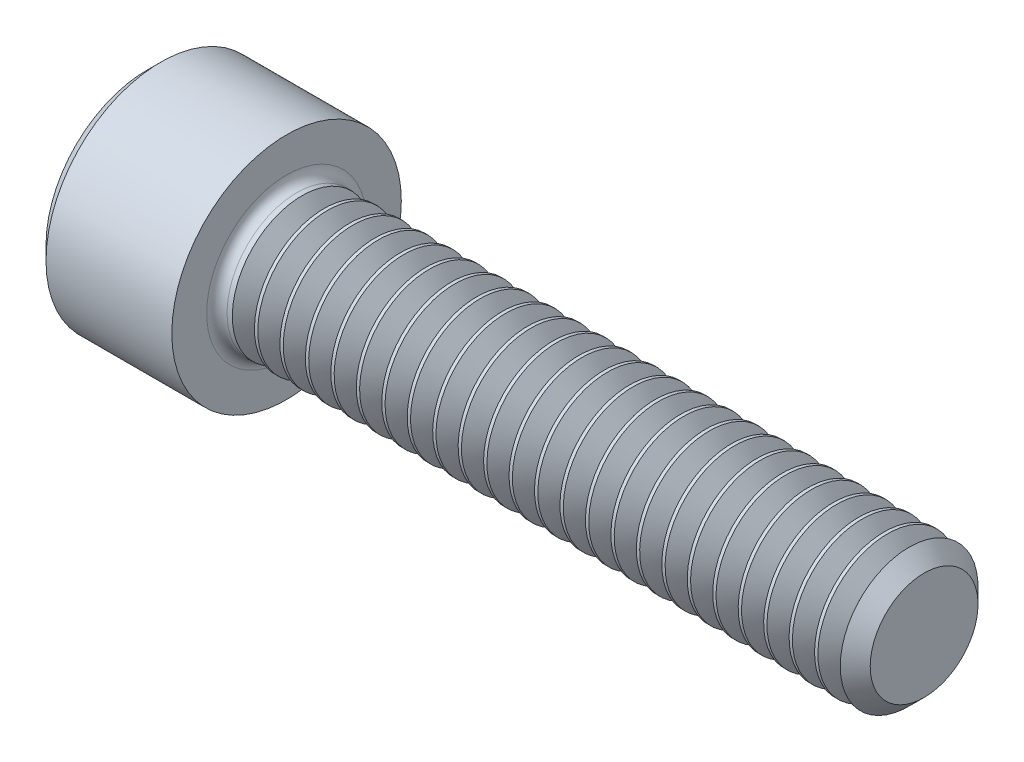
SolidWorks part; units mm, degrees
ref_plane "Plane1" through (0, 0, 0) normal (0, 0, 1) x (1, 0, 0)
ref_plane "Plane2" through (0, 0, 0) normal (0, 1, 0) x (1, 0, 0)
ref_plane "Plane3" through (0, 0, 0) normal (1, 0, 0) x (0, 0, -1)
sketch "BodySke" plane through (0, 0, 0) normal (0, 0, 1) x (1, 0, 0)
  line L0 (0, 0) -> (0, 3.0226)
  line L1 (0.4064, 3.429) -> (4.1656, 3.429)
  line L2 (4.1656, 3.429) -> (4.1656, 2.0828)
  line L3 (4.1656, 2.0828) -> (22.7432, 2.0828)
  line L4 (23.2156, 1.6104) -> (23.2156, 0)
  line L5 (23.2156, 0) -> (0, 0)
  line L6 (-31.75, 0) -> (127, 0) construction
  line L7 (0, 3.0226) -> (0.4064, 3.429)
  line L8 (23.2156, 1.6104) -> (22.7432, 2.0828)
  line L9 (0, -3.0226) -> (0.4064, -3.429) construction
  line L10 (23.2156, -1.6104) -> (22.7432, -2.0828) construction
  line L11 (4.9581, 9.525) -> (4.9581, 3.175) construction
  line L12 (4.1656, 9.525) -> (4.1656, 3.175) construction
  line L13 (-14.8844, 9.525) -> (-14.8844, 3.175) construction
  dimension "Diameter" = 4.1656
  dimension "Head_ht" = 4.1656
  dimension "Length" = 19.05
  dimension "Body_ch_ang" = 45
  dimension "Head_dia" = 6.858
  dimension "Head_ch_ang" = 45
  dimension "Head_side_ht" = 3.7592
  dimension "Minor_dia" = 3.2207
  dimension "Advance" = 0.7925
  dimension "Thread_nom" = 19.05
  dimension "Thread_length" = 38.1
revolve "Base-Revolve" add sketch "BodySke"
cosmetic thread "ThreadCosmetic" [suppressed]
fillet "Fillet1" radius 0.3048 1 edges at (4.1656, 0, 2.0828)
sketch "Sketch2" plane through (0, 0, 0) normal (0, 0, 1) x (1, 0, 0)
  line L0 (0, 1.778) -> (1.9558, 1.778)
  line L1 (1.9558, 1.778) -> (2.9823, 0)
  line L2 (-31.75, 0) -> (127, 0) construction
  line L3 (2.9823, 0) -> (0, 0)
  line L4 (0, 0) -> (0, 1.778)
  line L5 (0, 3.0226) -> (0, -3.0226) construction
  line L6 (0, 0) -> (47.625, 0) construction
  line L7 (4.1656, -3.429) -> (4.1656, 3.429) construction
  dimension "D1" = 1.778
  dimension "D2" = 60
  dimension "Wall_thickness" = 2.2098
revolve "Hex-PreBroach" cut sketch "Sketch2" angle 360 about L6
sketch "Sketch3" plane through (0, 0, 0) normal (-1, 0, 0) x (0, 0.5, 0.866)
  line L0 (1.0265, 1.778) -> (-1.0265, 1.778)
  line L1 (-1.0265, 1.778) -> (-2.0531, 0)
  line L2 (1.0265, 1.778) -> (2.0531, 0)
  line L3 (1.0265, -1.778) -> (2.0531, 0)
  line L4 (1.0265, -1.778) -> (-1.0265, -1.778)
  line L5 (-1.0265, -1.778) -> (-2.0531, 0)
  dimension "D1" = 1.778
  dimension "D2" = 1.778
  dimension "Hex_size" = 3.556
extrude "Hex" cut sketch "Sketch3" against normal blind 1.9558
sketch "Sketch4" plane through (0, 0, 0) normal (-1, 0, 0) x (0, 0, 1)
  line L0 (0, 0) -> (2.1971, 0)
  line L1 (0, 0) -> (6.1484, 3.5498) construction
  line L2 (0, 0) -> (1.0985, 1.9027)
  line L3 (1.8302, 0.5287) -> (2.0897, 0.6786)
  line L4 (1.373, 1.3206) -> (1.6325, 1.4704)
  arc A0 (1.8302, 0.5287) -> (1.373, 1.3206) centre (0, 0) ccw
  arc A1 (2.1971, 0) -> (2.0897, 0.6786) centre (0, 0) ccw
  arc A2 (1.0985, 1.9027) -> (1.6325, 1.4704) centre (0, 0) cw
  dimension "D1" = 30
  dimension "Spline_n_dim" = 3.81
  dimension "Spline_m_dim" = 4.3942
  dimension "D2" = 60
  dimension "D3" = 0.4572
  dimension "Spline_p_dim" = 0.9144
extrude "Spline" [suppressed] cut sketch "Sketch4" against normal blind 1.9558
pattern_circular "CirPattern1" [suppressed] count 6 every 60
sketch "Sketch5" plane through (0, 0, 0) normal (0, 0, 1) x (1, 0, 0)
  line L0 (-31.75, 0) -> (127, 0) construction
  line L2 (0, 3.0226) -> (0, -3.0226) construction
  circle A0 centre (1.524, 0) radius 0.5905
  dimension "Drilled_hole_dia" = 1.1811
  dimension "Drilled_hole_loc" = 1.524
extrude "Hole" [suppressed] cut sketch "Sketch5" against normal through all and the other way through all
pattern_circular "Drilled-4" [suppressed] count 2 every 60
pattern_circular "Drilled-6" [suppressed] count 3 every 60
sketch "ThdSchSke" plane through (0, 0, 0) normal (0, 0, 1) x (1, 0, 0)
  line L0 (4.9581, -1.6104) -> (4.6273, -2.0828)
  line L1 (4.9581, -1.6104) -> (5.2889, -2.0828)
  line L2 (5.2889, -2.0828) -> (5.2889, -2.6035)
  line L3 (-3.175, 0) -> (5.1513, 0) construction
  line L5 (5.2889, -2.6035) -> (4.6273, -2.6035)
  line L6 (4.6273, -2.6035) -> (4.6273, -2.0828)
  line L7 (0, 3.0226) -> (0, -3.0226) construction
  dimension "Thread_minor" = 3.2207
  dimension "Diameter" = 4.1656
  dimension "Start" = 4.9581
  dimension "SideAngle" = 55
  dimension "VeeAngle" = 70
  dimension "Overcut" = 5.207
revolve "ThreadSchematic" cut sketch "ThdSchSke" angle 360 about L3
pattern_linear "ThdSchPat" count 24 spacing 0.7607 along (1, 0, 0) of "ThreadSchematic"
equation "\"D2@Sketch3\" = \"Hex_size@Sketch3\" / 2"
equation "\"D1@Sketch3\" = \"Hex_size@Sketch3\" / 2"
equation "\"D1@Sketch2\" = \"Hex_size@Sketch3\" / 2"
equation "\"D3@Sketch4\" = \"Spline_p_dim@Sketch4\" / 2"
equation "\"Thread_minor@ThreadCosmetic\"  =  \"Minor_dia@BodySke\""
equation "\"D2@CirPattern1\" = 360 / \"Num_teeth@CirPattern1\""
equation "\"Wall_thickness@Sketch2\" = \"Head_ht@BodySke\" - \"Key_eng@Hex\""
equation "\"Thread_length@ThreadCosmetic\" = ((sgn( (\"Length@BodySke\" - \"Advance@BodySke\" ) - \"Thread_nom@BodySke\" )-1)*( (\"Length@BodySke\" - \"Advance@BodySke\" ) - \"Thread_nom@BodySke\" ))/-2+ \"Thread_nom@BodySke\""
equation "\"Thread_minor@ThdSchSke\" = \"Minor_dia@BodySke\""
equation "\"Diameter@ThdSchSke\" = \"Diameter@BodySke\""
equation "\"Overcut@ThdSchSke\" = \"Diameter@BodySke\" * 1.25"
equation "\"Start@ThdSchSke\" = \"Head_ht@BodySke\" + \"Length@BodySke\" - \"Thread_length@ThreadCosmetic\"  '---Non-countersunk---"
equation "\"Num_threads@ThdSchPat\" = int( \"Thread_length@ThreadCosmetic\" / \"Advance@BodySke\" + 0.999 )  + 1"
equation "\"Advance@ThdSchPat\" = \"Thread_length@ThreadCosmetic\" /  (\"Num_threads@ThdSchPat\" - 1) 'relax it"
equation "\"Num_threads@ThdSchPat\" = \"Num_threads@ThdSchPat\" - sgn( \"Num_threads@ThdSchPat\" - 1) '---chamfered tips only---"
